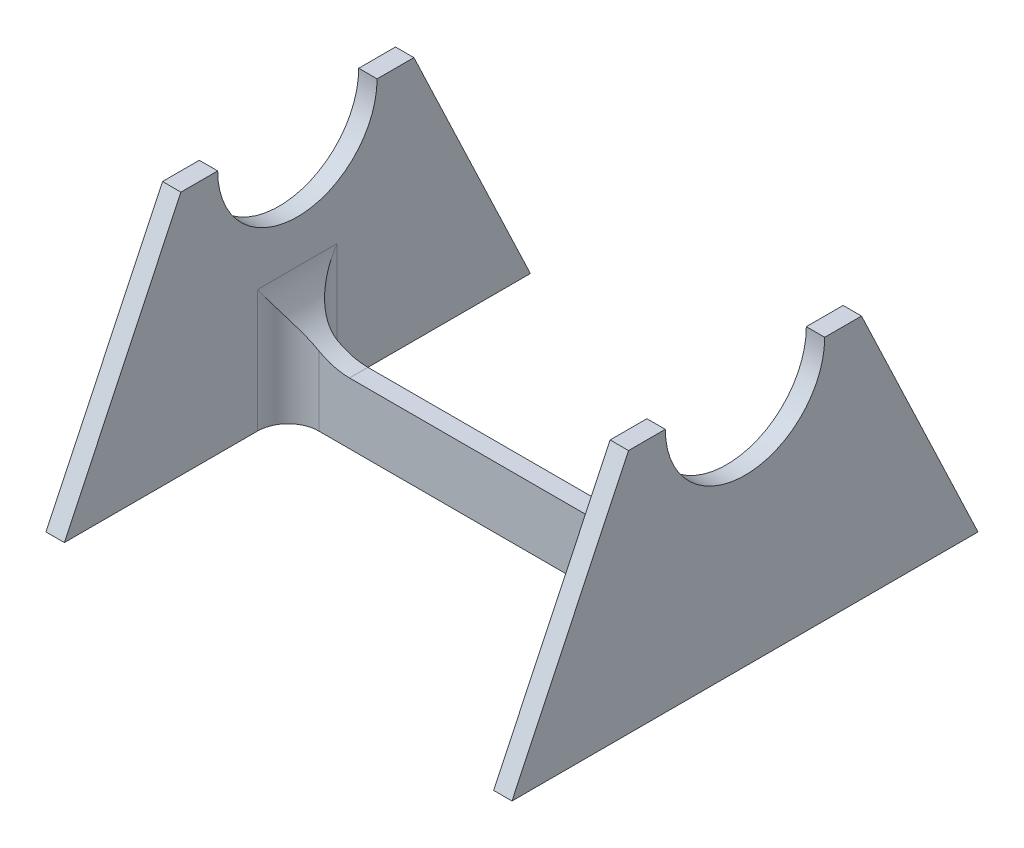
SolidWorks part; units mm, degrees
ref_plane "Plan de face" through (0, 0, 0) normal (0, 0, 1) x (1, 0, 0)
ref_plane "Plan de dessus" through (0, 0, 0) normal (0, 1, 0) x (1, 0, 0)
ref_plane "Plan de droite" through (0, 0, 0) normal (1, 0, 0) x (0, 0, -1)
sketch "Esquisse1" plane through (0, 0, 0) normal (0, 0, 1) x (1, 0, 0)
  line L1 (-35, -20) -> (35, -20)
  line L2 (-35, -20) -> (-35, 20)
  line L3 (-35, 20) -> (35, 20)
  line L4 (35, -20) -> (35, 20)
  line L5 (-35, -20) -> (35, 20) construction
  line L6 (-35, 20) -> (35, -20) construction
  point P0 (0, 0)
  dimension "D1" = 70
  dimension "D2" = 40
extrude "Boss.-Extru.1" add sketch "Esquisse1" along normal blind 3
sketch "Esquisse2" plane through (35, 0, 0) normal (1, 0, 0) x (0, 0, -1)
  line L0 (36.1664, 20) -> (-39.1664, 20) construction
  line L2 (-3, 20) -> (0, 20) construction
  line L3 (-1.5, 20) -> (-1.5, -16.078) construction
  line L4 (36.5, -20) -> (-39.5, -20) construction
  line L5 (-3, -20) -> (0, -20) construction
  line L6 (-14.5, 20) -> (-20.5, 20)
  line L7 (-20.5, 20) -> (-39.5, -20)
  line L12 (-7.9556, -20) -> (4.9556, -20)
  line L13 (-39.5, -20) -> (-36.0865, -20)
  line L16 (33.0865, -20) -> (4.9556, -20)
  line L17 (36.5, -20) -> (33.0865, -20)
  line L22 (-36.0865, -20) -> (-7.9556, -20)
  line L24 (17.5, 20) -> (36.5, -20)
  line L25 (11.5, 20) -> (17.5, 20)
  arc A0 (-1.5, 7) -> (-14.5, 20) centre (-1.5, 20) cw
  arc A1 (-1.5, 7) -> (11.5, 20) centre (-1.5, 20) ccw
  point P15 (-18.715, 14.5)
  point P16 (-36.8634, -18.9313)
  point P25 (-1.5, -20)
  dimension "D1" = 6
  dimension "D2" = 38
extrude "Boss.-Extru.2" add sketch "Esquisse2" along normal blind 3
mirror "Symétrie1" about plane through (0, 0, 0) normal (1, 0, 0) of "Boss.-Extru.2"
sketch "Esquisse3" plane through (0, 0, 3) normal (0, 0, 1) x (1, 0, 0)
  line L0 (35, 20) -> (-35, 20) construction
  line L1 (-35, 20) -> (35, 20)
  line L2 (-35, 20) -> (-35, -10)
  line L3 (-35, -10) -> (35, -10)
  line L4 (35, 20) -> (35, -10)
  line L5 (-35, 20) -> (-35, 7.0868) construction
  line L6 (35, -20) -> (35, 7.0868) construction
  dimension "D1" = 30
extrude "Enlèv. mat.-Extru.1" cut sketch "Esquisse3" against normal blind 3
fillet "Congé1" radius 10 2 edges at (-35, -10, 1.5) (35, -10, 1.5)
fillet "Congé2" radius 5 4 edges
